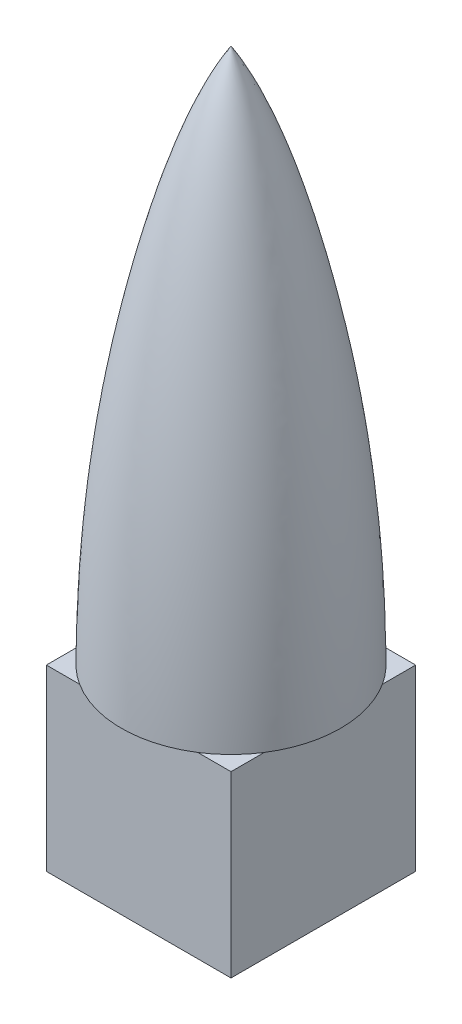
SolidWorks part; units mm, degrees
ref_plane "Front Plane" through (0, 0, 0) normal (0, 0, 1) x (1, 0, 0)
ref_plane "Top Plane" through (0, 0, 0) normal (0, 1, 0) x (1, 0, 0)
ref_plane "Right Plane" through (0, 0, 0) normal (1, 0, 0) x (0, 0, -1)
sketch "Sketch1" plane through (0, 0, 0) normal (0, 1, 0) x (1, 0, 0)
  line L1 (-7.75, -7.75) -> (7.75, -7.75)
  line L2 (-7.75, -7.75) -> (-7.75, 7.75)
  line L3 (-7.75, 7.75) -> (7.75, 7.75)
  line L4 (7.75, -7.75) -> (7.75, 7.75)
  line L5 (-7.75, -7.75) -> (7.75, 7.75) construction
  line L6 (-7.75, 7.75) -> (7.75, -7.75) construction
  point P0 (0, 0)
  dimension "D1" = 15.5
  dimension "D2" = 15.5
extrude "Boss-Extrude1" add sketch "Sketch1" along normal blind 15
sketch "Sketch2" plane through (0, 15, 0) normal (0, 1, 0) x (1, 0, 0)
  circle A0 centre (0, 0) radius 9.2
  point P3 (0, 0)
  dimension "D1" = 18.4
sketch "Sketch4" plane through (0, 0, 0) normal (0, 0, 1) x (1, 0, 0)
  line L0 (9.2, 15) -> (-9.2, 15) construction
  line L1 (9.2, 15) -> (0, 15)
  line L2 (0, 15) -> (0, 60)
  spline S0 degree 3 poles (9.2, 15) (9.1522, 24.691) (8.0098, 34.8825) (4.2472, 50.5068) (2.0168, 56.8059) (0, 60) knots 0 0 0 0 0.565415 0.665415 1 1 1 1
  point P6 (5.5401, 45.0928)
  dimension "D1" = 45
revolve "Revolve5" add sketch "Sketch4" angle 360 about L2
